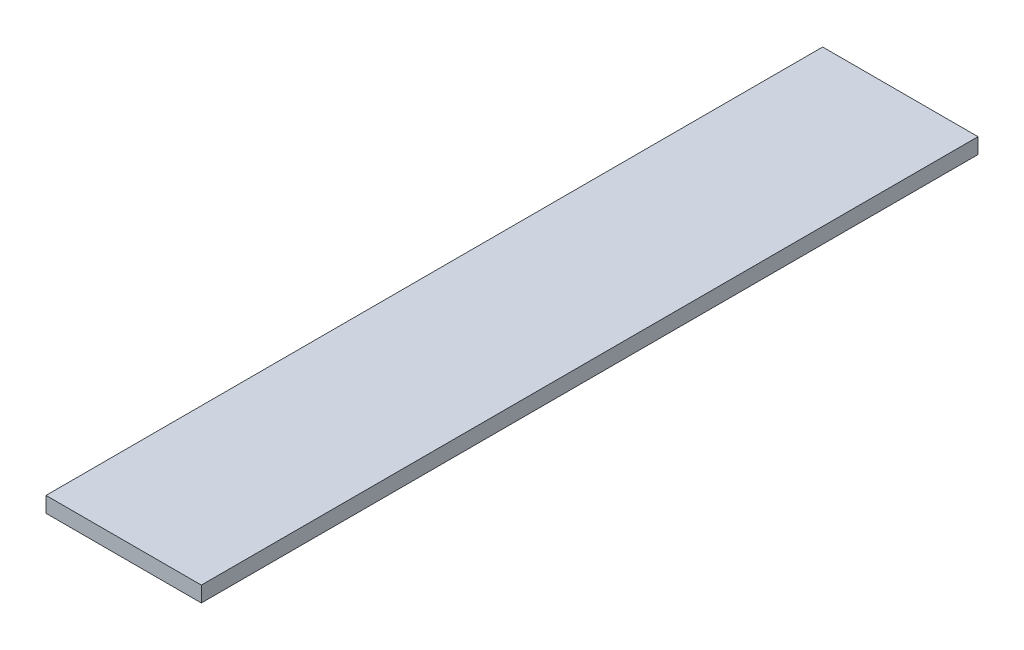
SolidWorks part; units mm, degrees
ref_plane "Front Plane" through (0, 0, 0) normal (0, 0, 1) x (1, 0, 0)
ref_plane "Top Plane" through (0, 0, 0) normal (0, 1, 0) x (1, 0, 0)
ref_plane "Right Plane" through (0, 0, 0) normal (1, 0, 0) x (0, 0, -1)
sketch "Sketch1" plane through (0, 0, 0) normal (0, 1, 0) x (1, 0, 0)
  line L1 (0, 0) -> (200, 0)
  line L2 (0, 0) -> (0, 1000)
  line L3 (0, 1000) -> (200, 1000)
  line L4 (200, 0) -> (200, 1000)
  dimension "D1" = 200
  dimension "D2" = 1000
extrude "Boss-Extrude1" add sketch "Sketch1" along normal blind 20
